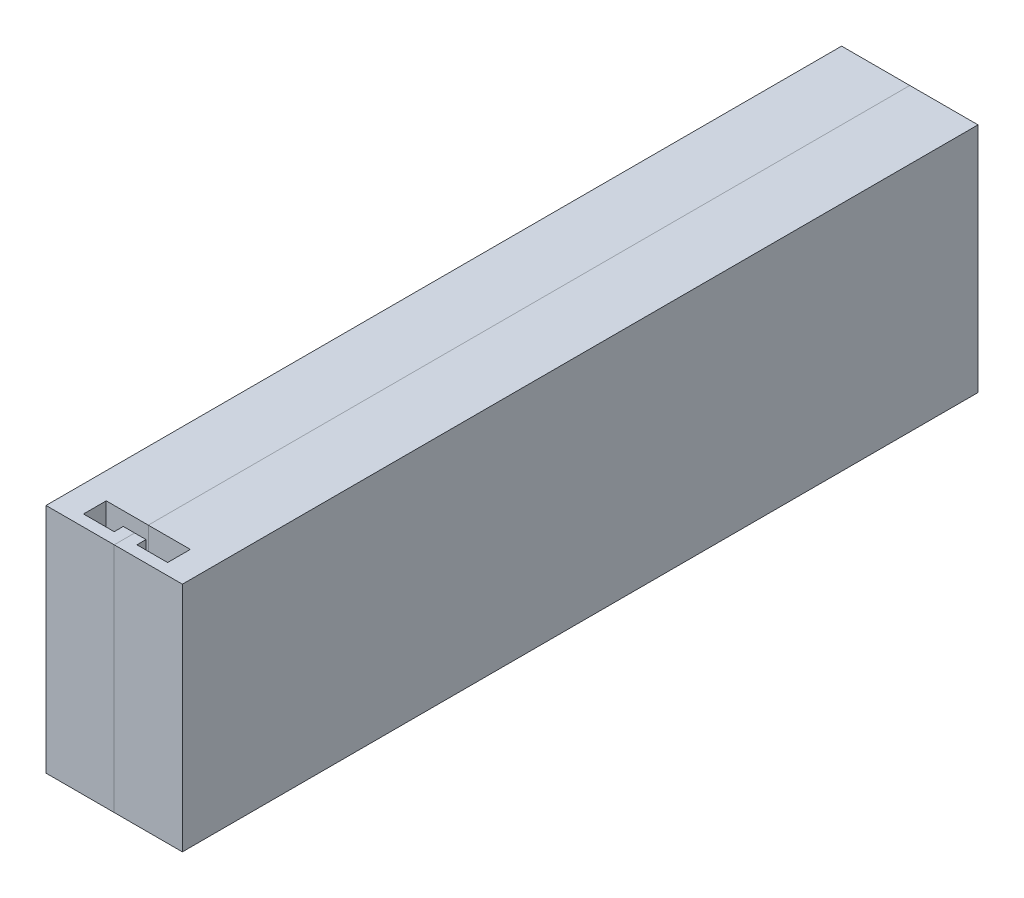
SolidWorks part; units mm, degrees
ref_plane "Front Plane" through (0, 0, 0) normal (0, 0, 1) x (1, 0, 0)
ref_plane "Top Plane" through (0, 0, 0) normal (0, 1, 0) x (1, 0, 0)
ref_plane "Right Plane" through (0, 0, 0) normal (1, 0, 0) x (0, 0, -1)
sketch "Sketch1" plane through (0, 0, 0) normal (1, 0, 0) x (0, 0, -1)
  line L1 (-64.5621, 30.5573) -> (110.4379, 30.5573)
  line L2 (-64.5621, 30.5573) -> (-64.5621, -20.4427)
  line L3 (-64.5621, -20.4427) -> (110.4379, -20.4427)
  line L4 (110.4379, 30.5573) -> (110.4379, -20.4427)
  dimension "D1" = 175
  dimension "D2" = 51
extrude "Boss-Extrude1" add sketch "Sketch1" along normal blind 15 contours L2 L3 L4 L1
sketch "Sketch6" plane through (0, 30.5573, 0) normal (0, 1, 0) x (1, 0, 0)
  line L0 (15, -64.5621) -> (15, -60.0621)
  line L1 (15, -64.5621) -> (15, 110.4379) construction
  line L2 (15, -60.0621) -> (15, -57.0621)
  line L3 (15, -57.0621) -> (12.5, -57.0621)
  line L4 (12.5, -57.0621) -> (5.75, -57.0621)
  line L5 (5.75, -57.0621) -> (5.75, -62.0621)
  line L6 (5.75, -62.0621) -> (12.5, -62.0621)
  line L7 (12.5, -62.0621) -> (12.5, -60.0621)
  line L8 (12.5, -60.0621) -> (15, -60.0621)
  line M11 (15, -64.5621) -> (15, 110.4379)
  dimension "D1" = 4.5
  dimension "D2" = 3
  dimension "D3" = 2.5
  dimension "D4" = 6.75
  dimension "D5" = 5
extrude "Cut-Extrude3" cut sketch "Sketch6" against normal through all contours L7 L8 L3 L4 L5 L6 M11
sketch "Sketch7" plane through (0, 0, -110.4379) normal (0, 0, -1) x (-1, 0, 0)
  line L0 (-15, -20.4427) -> (-15, -1.9427)
  line L1 (-15, 2.8073) -> (-15, 16.0573)
  line L2 (-10.25, 2.8073) -> (-15, 2.8073)
  line L3 (-10.25, 2.8073) -> (-10.25, -1.9427)
  line L4 (-10.25, -1.9427) -> (-15, -1.9427)
  line L5 (-15, 2.8073) -> (-15, -1.9427)
  line L6 (-15, 30.5573) -> (-15, -20.4427) construction
  line L8 (-15, 16.0573) -> (-10.25, 16.0573)
  line L9 (-15, 16.0573) -> (-15, 20.8073)
  line L10 (-15, 20.8073) -> (-10.25, 20.8073)
  line L11 (-10.25, 16.0573) -> (-10.25, 20.8073)
  line M6 (-15, 30.5573) -> (-15, -20.4427)
  dimension "D1" = 18.5
  dimension "D2" = 4.75
  dimension "D3" = 4.75
  dimension "D4" = 13.25
  dimension "D5" = 4.75
  dimension "D6" = 4.75
extrude "Cut-Extrude5" cut sketch "Sketch7" against normal blind 145 contours L4 L3 L2 M6 | L9 L8 L11 L10
sketch "Sketch10" plane through (0, 0, -110.4379) normal (0, 0, -1) x (-1, 0, 0)
  line L0 (-15, -20.4427) -> (-15, -2.4427)
  line L3 (-15, -2.4427) -> (-4.95, -2.4427)
  line L4 (-15, -2.4427) -> (-15, 21.5573)
  line L5 (-15, 21.5573) -> (-4.95, 21.5573)
  line L6 (-4.95, -2.4427) -> (-4.95, 21.5573)
  line M4 (-10.25, 2.8073) -> (-10.25, -1.9427)
  line M5 (-10.25, -1.9427) -> (-15, -1.9427)
  line M6 (-15, -1.9427) -> (-15, -20.4427)
  line M10 (-15, 30.5573) -> (-15, 20.8073)
  line M11 (-15, 2.8073) -> (-10.25, 2.8073)
  dimension "D1" = 18
  dimension "D2" = 24
  dimension "D3" = 10.05
extrude "Cut-Extrude6" cut sketch "Sketch10" against normal blind 16 contours L3 L6 L5 M10 M11 M4 M5 M6
sketch "Sketch11" plane through (0, -2.4427, 0) normal (0, 1, 0) x (1, 0, 0)
  line L0 (4.95, 94.4379) -> (4.95, 110.4379) construction
  line L1 (15, 94.4379) -> (4.95, 94.4379)
  line L2 (15, 94.4379) -> (15, 102.4879)
  line L3 (15, 102.4879) -> (4.95, 102.4879)
  line L4 (4.95, 94.4379) -> (4.95, 102.4879)
  dimension "D1" = 8.05
extrude "Cut-Extrude7" cut sketch "Sketch11" against normal blind 8
mirror "Mirror4" about plane through (15, 0, 0) normal (-1, 0, 0) of bodies 113 107
